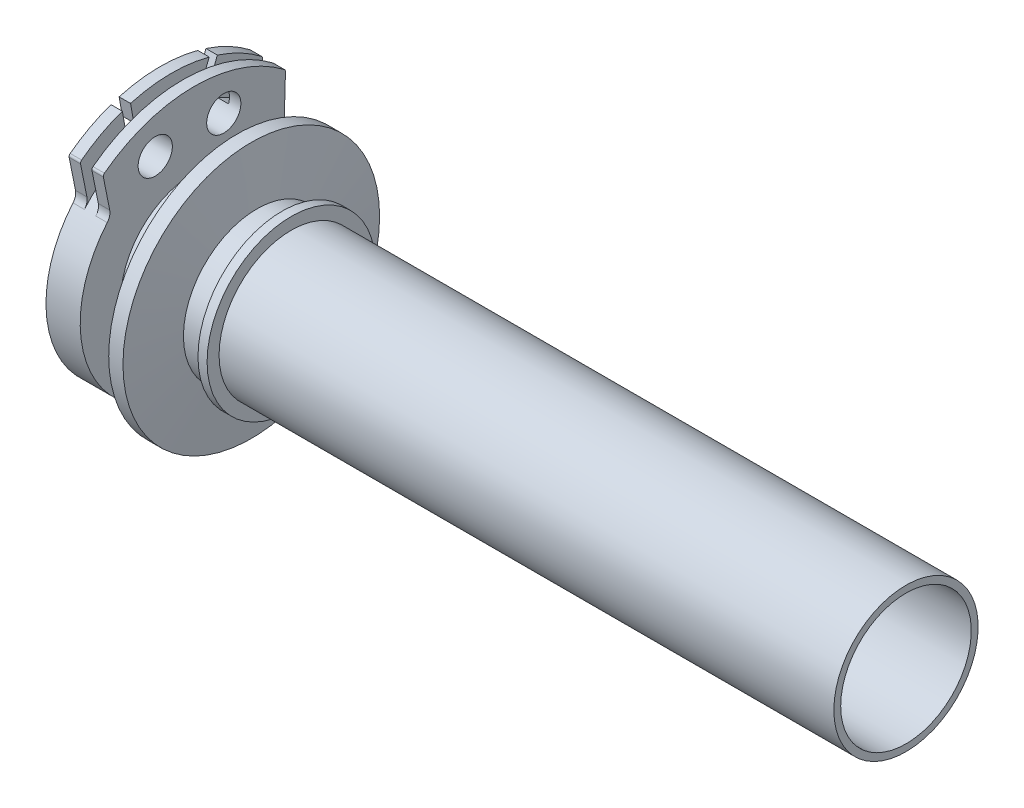
SolidWorks part; units mm, degrees
material "ABS"
ref_plane "Front Plane" through (0, 0, 0) normal (0, 0, 1) x (1, 0, 0)
ref_plane "Top Plane" through (0, 0, 0) normal (0, 1, 0) x (1, 0, 0)
ref_plane "Right Plane" through (0, 0, 0) normal (1, 0, 0) x (0, 0, -1)
sketch "Sketch1" plane through (0, 0, 0) normal (0, 0, 1) x (1, 0, 0)
  line L0 (130.8, 11.45) -> (0, 11.45)
  line L1 (0, -55) -> (0, 55) construction
  line L2 (0, 11.45) -> (0, 26)
  line L3 (0, 26) -> (6, 26)
  line L8 (6, 26) -> (6, 12.9)
  line L9 (6, 12.9) -> (10, 12.9)
  line L10 (10, 12.9) -> (10, 15.5)
  line L11 (10, 15.5) -> (12, 15.5)
  line L12 (12, 15.5) -> (12, 14)
  line L13 (23, 12.65) -> (130.8, 12.65)
  line L14 (130.8, 12.65) -> (130.8, 11.45)
  line L15 (0, 0) -> (64.5198, 0) construction
  line L16 (12, 14) -> (13, 14)
  line L17 (13, 14) -> (13.5, 22.5)
  line L18 (16, 22.5) -> (13.5, 22.5)
  line L19 (16, 22.5) -> (17, 12.9)
  line L20 (17, 12.9) -> (21.4, 12.9)
  line L21 (21.4, 12.9) -> (21.4, 14.75)
  line L22 (21.4, 14.75) -> (23, 14.75)
  line L23 (23, 14.75) -> (23, 12.65)
  dimension "D1" = 22.9
  dimension "D2" = 25.3
  dimension "D3" = 130.8
  dimension "D4" = 52
  dimension "D5" = 6
  dimension "D7" = 4
  dimension "D8" = 2
  dimension "D11" = 25.8
  dimension "D12" = 31
  dimension "D13" = 1
  dimension "D14" = 13.5
  dimension "D15" = 16
  dimension "D16" = 45
  dimension "D17" = 1.5
  dimension "D18" = 17
  dimension "D19" = 23
  dimension "D20" = 1.6
  dimension "D21" = 29.5
revolve "Revolve1" add sketch "Sketch1" angle 360 about L15
sketch "Sketch5" plane through (0, 0, 0) normal (0, 0, 1) x (1, 0, 0)
  line L1 (2, 20) -> (4, 20)
  line L2 (2, 20) -> (2, 45)
  line L3 (2, 45) -> (4, 45)
  line L4 (4, 20) -> (4, 45)
  line L5 (0, 26) -> (0, -26) construction
  line L7 (0, 0) -> (-14.4458, 0) construction
  dimension "D1" = 2
  dimension "D2" = 2
  dimension "D3" = 40
revolve "Cut-Revolve1" cut sketch "Sketch5" angle 360 about L7
sketch "Sketch2" plane through (0, 0, 0) normal (-1, 0, 0) x (0, 0, 1)
  line L0 (14.6271, 13.64) -> (16, 20.4939)
  line L1 (-15.7602, 12.3132) -> (-16, 20.4939)
  line L2 (0, 0) -> (0, 26) construction
  line L3 (-16, 20.4939) -> (16, 20.4939) construction
  line L4 (-5.1764, 19.3185) -> (0, 0) construction
  line L5 (-5.1764, 19.3185) -> (6.8404, 18.7939) construction
  line L6 (0, 0) -> (6.8404, 18.7939) construction
  line L7 (0, 0) -> (-15.7602, 12.3132) construction
  line L8 (0, 0) -> (14.6271, 13.64) construction
  circle A0 centre (0, 0) radius 20 construction
  arc A1 (-16, 20.4939) -> (16, 20.4939) centre (0, 0) ccw
  arc A4 (-15.7602, 12.3132) -> (14.6271, 13.64) centre (0, 0) ccw
  circle A5 centre (0, 0) radius 26 construction
  circle A6 centre (-5.1764, 19.3185) radius 3
  circle A7 centre (6.8404, 18.7939) radius 3
  circle A8 centre (0, 0) radius 20 construction
  dimension "D4" = 15
  dimension "D6" = 6
  dimension "D1" = 20
  dimension "D2" = 88.321
  dimension "D3" = 78.673
  dimension "D7" = 32
  dimension "D8" = 20
extrude "Cut-Extrude1" cut sketch "Sketch2" against normal up to surface (6 mm away) up to face at (6, 0, 26)
fillet "Fillet1" radius 2 4 edges at (5, 12.3132, -15.7602) (1, 12.3132, -15.7602) (5, 13.64, 14.6271) (1, 13.64, 14.6271)
sketch "Sketch3" plane through (0, 0, 0) normal (-1, 0, 0) x (0, 0, 1)
  line L0 (-16.9683, -1.0378) -> (-19.9955, -0.4219)
  line L1 (2.5128, -16.8133) -> (3.7446, -19.6463)
  line L2 (0, -26.675) -> (0, 26.675) construction
  line L4 (-16.9683, -1.0378) -> (0, 0) construction
  line L5 (0, 0) -> (2.5128, -16.8133) construction
  arc A1 (-16.9683, -1.0378) -> (2.5128, -16.8133) centre (0, 0) ccw
  arc A2 (-16.1636, 11.7787) -> (15.2579, 12.9304) centre (0, 0) ccw construction
  arc A4 (-19.9955, -0.4219) -> (3.7446, -19.6463) centre (0, 0) ccw
  dimension "D5" = 17
  dimension "D1" = 95
  dimension "D2" = 165
  dimension "D3" = 165
  dimension "D4" = 8.5
extrude "Cut-Extrude2" cut sketch "Sketch3" against normal up to surface (6 mm away) up to face at (6, 18.7939, 9.8404)
fillet "Fillet2" radius 0.5 6 edges at (3, -19.6463, 3.7446) (3, -0.4219, -19.9955) (5, 20.4939, 16) (1, 20.4939, 16) (1, 20.4939, -16) (5, 20.4939, -16)
sketch "Sketch4" plane through (0, 0, 0) normal (-1, 0, 0) x (0, 0, 1)
  line L0 (-5.8434, 18.9756) -> (-4.5094, 19.6614)
  line L1 (-5.8434, 18.9756) -> (-11.8144, 34.5307)
  line L2 (-4.5094, 19.6614) -> (-10.4804, 35.2165)
  line L3 (-11.8144, 34.5307) -> (-10.4804, 35.2165)
  line L4 (6.1084, 18.9574) -> (7.5724, 18.6303)
  line L5 (6.1084, 18.9574) -> (9.076, 35.7875)
  line L6 (7.5724, 18.6303) -> (10.54, 35.4604)
  line L7 (9.076, 35.7875) -> (10.54, 35.4604)
  line L8 (-5.1764, 19.3185) -> (-11.1474, 34.8736) construction
  line L9 (6.8404, 18.7939) -> (9.808, 35.6239) construction
  line L11 (0, 2.2774) -> (0, 8.6826) construction
  circle A0 centre (6.8404, 18.7939) radius 3 construction
  point P11 (-5.1764, 19.3185)
  dimension "D1" = 1.5
  dimension "D2" = 1.5
  dimension "D3" = 21
  dimension "D4" = 10
extrude "Cut-Extrude3" cut sketch "Sketch4" against normal up to next
